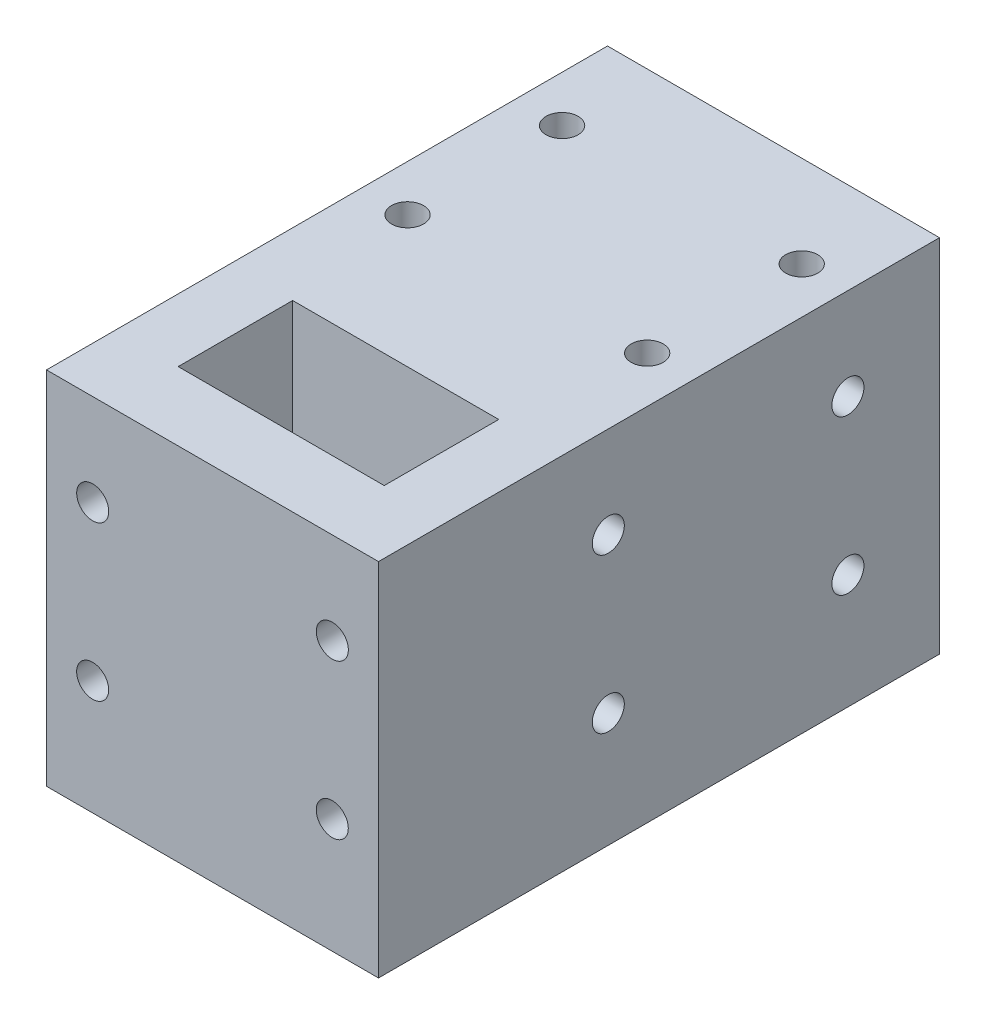
SolidWorks part; units mm, degrees
material "Copper"
ref_plane "Front Plane" through (0, 0, 0) normal (0, 0, 1) x (1, 0, 0)
ref_plane "Top Plane" through (0, 0, 0) normal (0, 1, 0) x (1, 0, 0)
ref_plane "Right Plane" through (0, 0, 0) normal (1, 0, 0) x (0, 0, -1)
sketch "Sketch1" plane through (0, 0, 0) normal (0, 1, 0) x (1, 0, 0)
  line L1 (-17.21, 33.6238) -> (11.79, 33.6238)
  line L2 (-17.21, 33.6238) -> (-17.21, -15.3762)
  line L3 (-17.21, -15.3762) -> (11.79, -15.3762)
  line L4 (11.79, 33.6238) -> (11.79, -15.3762)
  dimension "D1" = 49
  dimension "D2" = 29
extrude "Boss-Extrude1" add sketch "Sketch1" along normal blind 31.5
sketch "Sketch2" plane through (0, 31.5, 0) normal (0, 1, 0) x (1, 0, 0)
  line L1 (-2.71, 33.6238) -> (-2.71, -15.3762) construction
  line L2 (11.79, 33.6238) -> (-17.21, 33.6238) construction
  line L3 (-17.21, -15.3762) -> (11.79, -15.3762) construction
  line L6 (-11.71, 0.6238) -> (6.29, 0.6238)
  line L7 (-11.71, 0.6238) -> (-11.71, -9.3762)
  line L8 (-11.71, -9.3762) -> (6.29, -9.3762)
  line L9 (6.29, 0.6238) -> (6.29, -9.3762)
  dimension "D1" = 33
  dimension "D2" = 18
  dimension "D3" = 10
  dimension "D4" = 9
extrude "Cut-Extrude1" cut sketch "Sketch2" against normal through all
sketch "Sketch3" plane through (0, 31.5, 0) normal (0, 1, 0) x (1, 0, 0)
  line L0 (11.79, 33.6238) -> (-17.21, 33.6238) construction
  line L3 (6.29, 0.6238) -> (-11.71, 0.6238) construction
  circle A0 centre (-13.175, 25.6238) radius 1.4
  circle A1 centre (-13.175, 12.1238) radius 1.4
  circle A2 centre (7.755, 25.6238) radius 1.4
  circle A3 centre (7.755, 12.1238) radius 1.4
  point P12 (-2.71, 0.6238)
  dimension "D1" = 2.8
  dimension "D2" = 8
  dimension "D4" = 2.8
  dimension "D5" = 8
  dimension "D6" = 13.5
  dimension "D7" = 2.8
  dimension "D8" = 2.8
  dimension "D9" = 20.93
  dimension "D10" = 20.93
  dimension "D11" = 13.5
  dimension "D3" = 10.465
extrude "Cut-Extrude2" cut sketch "Sketch3" against normal blind 3.4
ref_plane "Plane2" through (-2.71, 0, 0) normal (-1, 0, 0) x (0, 0, 1)
sketch "Sketch4" plane through (-17.21, 0, 0) normal (-1, 0, 0) x (0, 0, 1)
  line L0 (-33.6238, 31.5) -> (15.3762, 31.5) construction
  line L1 (-33.6238, 31.5) -> (-33.6238, 0) construction
  circle A0 centre (-25.6238, 23.5) radius 1.4
  circle A1 centre (-4.6938, 23.5) radius 1.4
  circle A2 centre (-25.6238, 10) radius 1.4
  circle A3 centre (-4.6938, 10) radius 1.4
  dimension "D1" = 2.8
  dimension "D2" = 2.8
  dimension "D3" = 2.8
  dimension "D4" = 2.8
  dimension "D5" = 8
  dimension "D6" = 8
  dimension "D7" = 8
  dimension "D8" = 8
  dimension "D9" = 13.5
  dimension "D10" = 13.5
  dimension "D11" = 20.93
  dimension "D12" = 20.93
extrude "Cut-Extrude3" cut sketch "Sketch4" against normal blind 3.4
mirror "Mirror1" about plane through (-2.71, 0, 0) normal (-1, 0, 0) of "Cut-Extrude3"
sketch "Sketch5" plane through (0, 0, 15.3762) normal (0, 0, 1) x (1, 0, 0)
  line L0 (-2.71, 17.325) -> (-2.71, -17.325) construction
  line L1 (-17.21, 31.5) -> (11.79, 31.5) construction
  circle A0 centre (-13.175, 23.5) radius 1.4
  circle A1 centre (7.755, 23.5) radius 1.4
  circle A2 centre (-13.18, 10) radius 1.4
  circle A3 centre (7.75, 10) radius 1.4
  dimension "D1" = 2.8
  dimension "D2" = 2.8
  dimension "D3" = 2.8
  dimension "D4" = 2.8
  dimension "D5" = 20.93
  dimension "D6" = 10.465
  dimension "D7" = 20.93
  dimension "D8" = 10.47
  dimension "D9" = 13.5
  dimension "D10" = 13.5
  dimension "D11" = 8
  dimension "D12" = 8
extrude "Cut-Extrude4" cut sketch "Sketch5" against normal blind 3.4
ref_plane "Plane3" through (0, 0, -9.1238) normal (0, 0, 1) x (1, 0, 0)
mirror "Mirror2" about plane through (0, 0, -9.1238) normal (0, 0, 1) of "Cut-Extrude4"
ref_plane "Plane5" through (0, 0, -0.6238) normal (0, 0, 1) x (1, 0, 0)
sketch "Sketch7" plane through (0, 0, 0) normal (0, -1, 0) x (1, 0, 0)
  line L0 (-17.21, -0.6238) -> (11.79, -33.6238) construction
  line L1 (-17.21, -33.6238) -> (-17.21, 15.3762) construction
  line L2 (11.79, 15.3762) -> (11.79, -33.6238) construction
  line L4 (16.5, -0.6238) -> (-16.5, -0.6238) construction
  line L5 (11.79, -0.6238) -> (-17.21, -0.6238) construction
  line L6 (3.9295, -17.1238) -> (0.6097, -11.3738)
  line L7 (0.6097, -11.3738) -> (-6.0298, -11.3738)
  line L8 (-6.0298, -11.3738) -> (-9.3496, -17.1238)
  line L9 (-9.3496, -17.1238) -> (-6.0298, -22.8738)
  line L10 (-6.0298, -22.8738) -> (0.6097, -22.8738)
  line L11 (0.6097, -22.8738) -> (3.9295, -17.1238)
  circle A0 centre (-2.71, -17.1238) radius 5.75 construction
  dimension "D1" = 11.5
extrude "Cut-Extrude5" cut sketch "Sketch7" against normal blind 12
